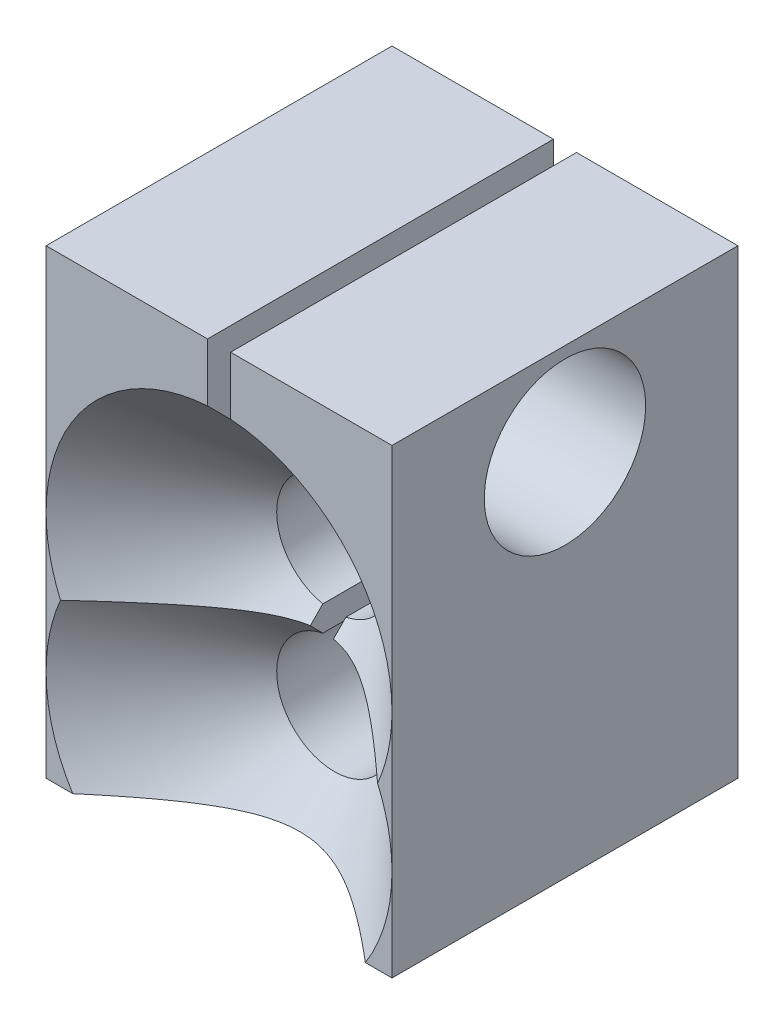
SolidWorks part; units mm, degrees
material "Mosiądz"
ref_plane "Płaszczyzna przednia" through (0, 0, 0) normal (0, 0, 1) x (1, 0, 0)
ref_plane "Płaszczyzna górna" through (0, 0, 0) normal (0, 1, 0) x (1, 0, 0)
ref_plane "Płaszczyzna prawa" through (0, 0, 0) normal (1, 0, 0) x (0, 0, -1)
sketch "Szkic1" plane through (0, 0, 0) normal (0, 1, 0) x (1, 0, 0)
  line L1 (-7.5, -7.5) -> (7.5, -7.5)
  line L2 (-7.5, -7.5) -> (-7.5, 7.5)
  line L3 (-7.5, 7.5) -> (7.5, 7.5)
  line L4 (7.5, -7.5) -> (7.5, 7.5)
  line L5 (-7.5, -7.5) -> (7.5, 7.5) construction
  line L6 (-7.5, 7.5) -> (7.5, -7.5) construction
  point P0 (0, 0)
  dimension "D1" = 15
  dimension "D2" = 15
extrude "Dodanie-wyciągnięcie1" add sketch "Szkic1" along normal blind 20
sketch "Szkic2" plane through (0, 0, 7.5) normal (0, 0, 1) x (1, 0, 0)
  line L1 (-7.5, 0) -> (7.5, 0) construction
  circle A0 centre (0, 4) radius 2.5
  circle A1 centre (0, 10) radius 2.5
  dimension "D1" = 4
  dimension "D2" = 10
  dimension "D3" = 5
sketch "Szkic3" plane through (0, 0, 7.5) normal (0, 0, 1) x (1, 0, 0)
  line L0 (-7.5, 20) -> (7.5, 20) construction
  line L1 (-0.5, 20) -> (0.5, 20)
  line L2 (-0.5, 20) -> (-0.5, 6.4222)
  line L3 (-0.5, 6.4222) -> (0.5, 6.4222)
  line L4 (0.5, 20) -> (0.5, 6.4222)
  line L6 (0.5, 6.4222) -> (-0.5, 6.4222)
  line L7 (0.5, 6.4222) -> (0.5, 20)
  line L8 (0.5, 20) -> (-0.5, 20)
  line L9 (-0.5, 6.4222) -> (-0.5, 20)
  point P6 (0, 20)
  point P7 (0, 20)
  line M8 (7.5, 20) -> (-7.5, 20)
  dimension "D1" = 1
sketch "Szkic4" plane through (7.5, 0, 0) normal (1, 0, 0) x (0, 0, -1)
  line L0 (-7.5, 20) -> (7.5, 20) construction
  circle A0 centre (0, 16) radius 1.5
  dimension "D1" = 4
hole_wizard "Pogłębienie walcowe pod M3 wkręt do części metalowych z łbem stożkowym ściętym2" positions "Szkic7" profile "Szkic8" counterbore size "M3" standard "Ansi Metric" end condition through all
sketch "Szkic7" plane through (7.5, 0, 0) normal (1, 0, 0) x (0, 0, -1)
  point P0 (0, 16)
sketch "Szkic8" plane through (7.5, 16, 0) normal (0, 1, 0) x (0, 0, -1)
  line L0 (0, 0) -> (0, 15)
  line L1 (0, 15) -> (1.8, 15)
  line L3 (1.8, 15) -> (1.8, 5)
  line L4 (1.8, 5) -> (3.5, 5)
  line L5 (3.5, 5) -> (3.5, 0)
  line L7 (3.5, 0) -> (0, 0)
  line L11 (0, -6.35) -> (0, 107.95) construction
  dimension "Średnica otworu na wylot" = 3.6
  dimension "Głębokość otworu na wylot" = 15
  dimension "Średnica pogłębienia walcowego" = 7
  dimension "Głębokość pogłębienia walcowego" = 5
hole_wizard "Pogłębienie stożkowe pod M5 wkręt do części metalowych z łbem soczewkowym1" positions "Szkic9" profile "Szkic11" countersink size "M5" standard "Ansi Metric" end condition through all
sketch "Szkic9" plane through (0, 0, 7.5) normal (0, 0, 1) x (1, 0, 0)
  point P0 (0, 10)
  point P3 (0, 4)
sketch "Szkic11" plane through (0, 10, 7.5) normal (1, 0, 0) x (0, -1, 0)
  line L0 (0, 0) -> (0, 15)
  line L1 (0, 15) -> (2.5, 15)
  line L2 (2.5, 15) -> (2.5, 5)
  line L3 (2.5, 5) -> (7.5, 0)
  line L5 (7.5, 0) -> (0, 0)
  line L6 (-2.5, 5) -> (-7.5, 0) construction
  line L11 (0, -6.35) -> (0, 107.95) construction
  dimension "Średnica otworu na wylot" = 5
  dimension "Głębokość otworu na wylot" = 15
  dimension "Średnica zewnętrznego pogłębienia stożkowego" = 15
  dimension "Kąt zewnętrznego pogłębienia stożkowego" = 90
extrude "Wytnij-wyciągnięcie1" cut sketch "Szkic3" against normal through all contours L4 L2 L3 M8
